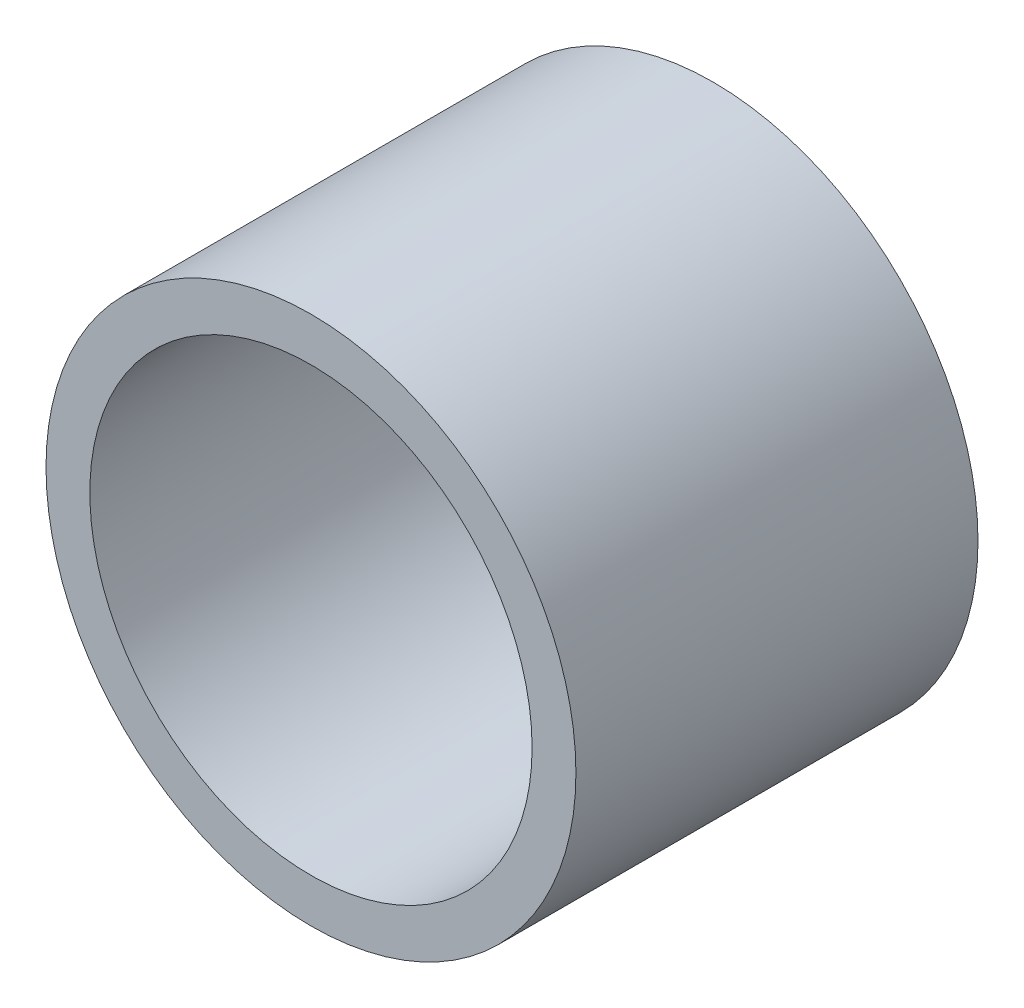
SolidWorks part; units mm, degrees
material "ABS"
ref_plane "Front Plane" through (0, 0, 0) normal (0, 0, 1) x (1, 0, 0)
ref_plane "Top Plane" through (0, 0, 0) normal (0, 1, 0) x (1, 0, 0)
ref_plane "Right Plane" through (0, 0, 0) normal (1, 0, 0) x (0, 0, -1)
sketch "Sketch1" plane through (0, 0, 0) normal (0, 0, 1) x (1, 0, 0)
  circle A0 centre (0, 0) radius 27.5
  circle A1 centre (0, 0) radius 32.95
  dimension "D1" = 65.9
  dimension "D2" = 55
extrude "Boss-Extrude1" add sketch "Sketch1" along normal blind 50
